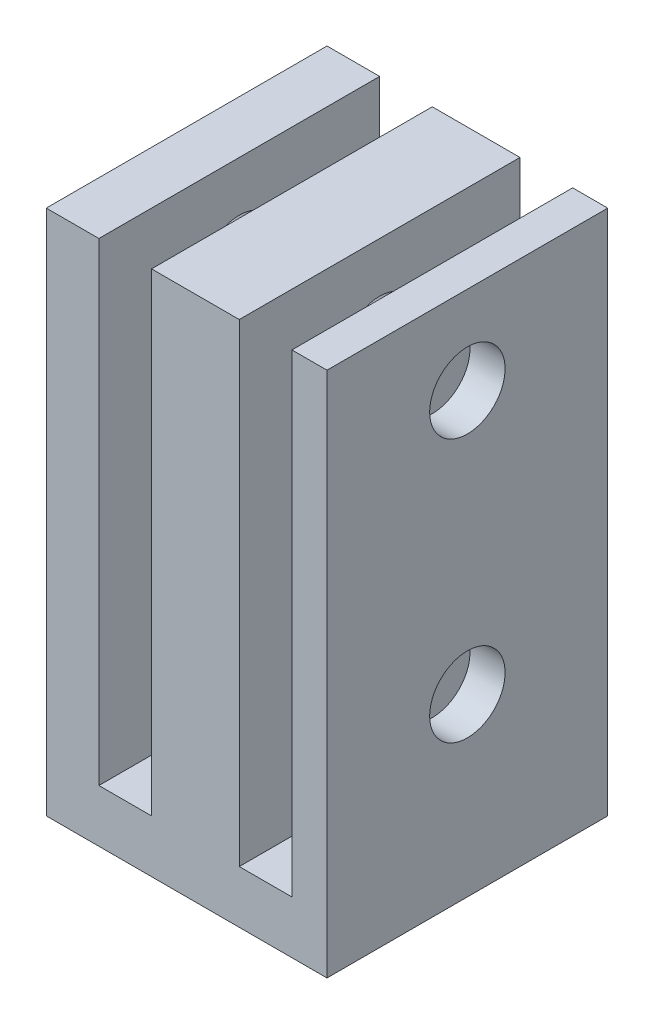
SolidWorks part; units mm, degrees
ref_plane "Front Plane" through (0, 0, 0) normal (0, 0, 1) x (1, 0, 0)
ref_plane "Top Plane" through (0, 0, 0) normal (0, 1, 0) x (1, 0, 0)
ref_plane "Right Plane" through (0, 0, 0) normal (1, 0, 0) x (0, 0, -1)
sketch "Sketch1" plane through (0, 0, 0) normal (0, 1, 0) x (1, 0, 0)
  line L1 (0, 0) -> (16, 0)
  line L2 (0, 0) -> (0, 16)
  line L3 (0, 16) -> (16, 16)
  line L4 (16, 0) -> (16, 16)
  dimension "D1" = 16
extrude "Boss-Extrude1" add sketch "Sketch1" along normal blind 30
sketch "Sketch2" plane through (0, 0, 0) normal (0, 0, 1) x (1, 0, 0)
  line L0 (0, 30) -> (16, 30) construction
  line L1 (3, 30) -> (6, 30)
  line L2 (3, 30) -> (3, 3)
  line L3 (3, 3) -> (6, 3)
  line L4 (6, 30) -> (6, 3)
  line L6 (11, 30) -> (14, 30)
  line L7 (11, 30) -> (11, 3)
  line L8 (11, 3) -> (14, 3)
  line L9 (14, 30) -> (14, 3)
  line L10 (0, 30) -> (0, 0) construction
  line L11 (0, 0) -> (16, 0) construction
  dimension "D1" = 5
  dimension "D2" = 3
  dimension "D3" = 3
  dimension "D4" = 3
extrude "Cut-Extrude1" cut sketch "Sketch2" against normal through all
sketch "Sketch3" plane through (0, 0, 0) normal (-1, 0, 0) x (0, 0, 1)
  line L0 (0, 30) -> (0, 0) construction
  line L2 (-16, 0) -> (0, 0) construction
  circle A0 centre (-8, 25) radius 2.15
  circle A1 centre (-8, 10) radius 2.15
  dimension "D1" = 4.3
  dimension "D2" = 8
  dimension "D3" = 15
  dimension "D4" = 10
extrude "Cut-Extrude2" cut sketch "Sketch3" against normal through all
